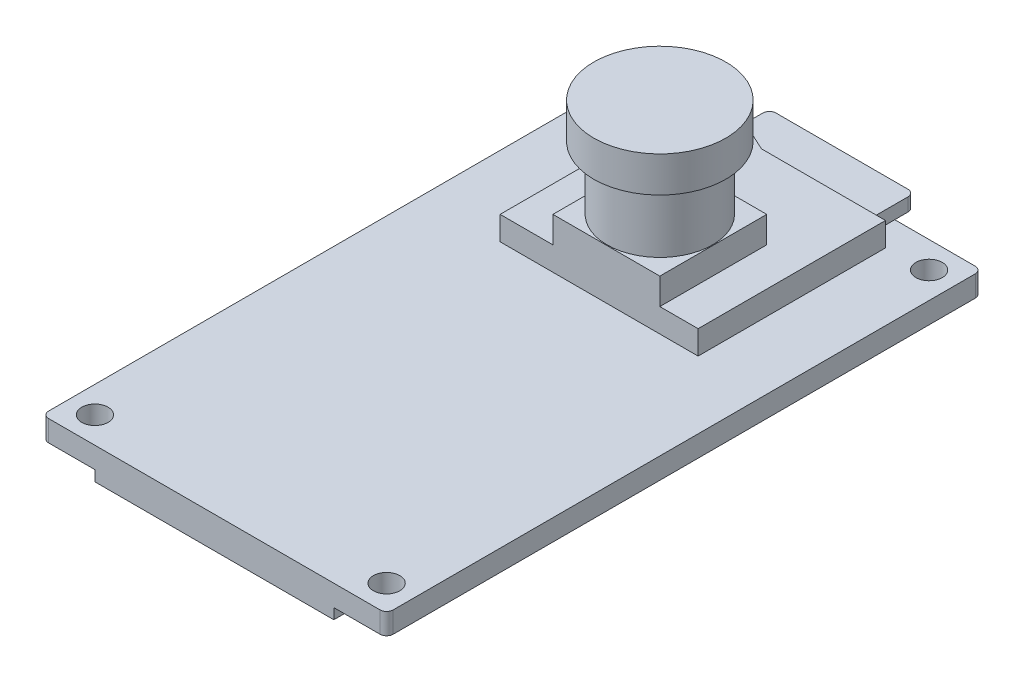
SolidWorks part; units mm, degrees
ref_plane "前视基准面" through (0, 0, 0) normal (0, 0, 1) x (1, 0, 0)
ref_plane "上视基准面" through (0, 0, 0) normal (0, 1, 0) x (1, 0, 0)
ref_plane "右视基准面" through (0, 0, 0) normal (1, 0, 0) x (0, 0, -1)
sketch "草图1" plane through (0, 0, 0) normal (0, 1, 0) x (1, 0, 0)
  line L0 (0, 60.3129) -> (0, -70.9474) construction
  line L1 (-96.3183, 0) -> (97.2298, 0) construction
  line L2 (-13.05, 22.55) -> (-13.05, -22.55)
  line L3 (-13.05, -22.55) -> (13.05, -22.55)
  line L4 (13.05, -22.55) -> (13.05, 22.55)
  line L5 (13.05, 22.55) -> (-13.05, 22.55)
  circle A0 centre (-11.05, 20.55) radius 1
  circle A1 centre (11.05, 20.55) radius 1
  circle A2 centre (-11.05, -20.55) radius 1
  circle A3 centre (11.05, -20.55) radius 1
  dimension "D5" = 2
  dimension "D1" = 26.1
  dimension "D2" = 45.1
  dimension "D3" = 22.1
  dimension "D4" = 41.1
extrude "凸台-拉伸1" add sketch "草图1" along normal blind 1.6
sketch "草图2" plane through (0, 1.6, 0) normal (0, 1, 0) x (1, 0, 0)
  line L0 (-7.05, 6.15) -> (7.95, 6.15)
  line L1 (7.95, 6.15) -> (7.95, 20.35)
  line L2 (7.95, 20.35) -> (-1.45, 20.35)
  line L3 (-1.45, 20.35) -> (-2.75, 20.95)
  line L4 (-2.75, 20.95) -> (-7.05, 20.95)
  line L5 (-7.05, 20.95) -> (-7.05, 6.15)
  line L6 (13.05, 22.55) -> (-13.05, 22.55) construction
  line L7 (13.05, -22.55) -> (13.05, 22.55) construction
  dimension "D1" = 14.2
  dimension "D2" = 14.8
  dimension "D3" = 15
  dimension "D4" = 9.4
  dimension "D5" = 4.3
  dimension "D6" = 1.6
  dimension "D7" = 5.1
extrude "凸台-拉伸2" add sketch "草图2" along normal blind 1.8
sketch "草图3" plane through (0, 0, -20.35) normal (0, 0, -1) x (-1, 0, 0)
  line L0 (-7.15, 2.3) -> (-7.15, 3.3)
  line L1 (-7.15, 3.3) -> (3.85, 3.3)
  line L2 (3.85, 3.3) -> (3.85, 2.3)
  line L3 (3.85, 2.3) -> (-7.15, 2.3)
  line L4 (-7.95, 3.4) -> (-7.95, 1.6) construction
  line L5 (-7.95, 3.4) -> (1.45, 3.4) construction
  dimension "D1" = 0.8
  dimension "D2" = 1
  dimension "D3" = 0.1
  dimension "D4" = 11
extrude "凸台-拉伸3" add sketch "草图3" along normal blind 3
fillet "圆角1" radius 0.5 6 edges at (-3.85, 2.8, -23.35) (7.15, 2.8, -23.35) (-13.05, 0.8, 22.55) (13.05, 0.8, 22.55) (13.05, 0.8, -22.55) (-13.05, 0.8, -22.55)
sketch "草图4" plane through (0, 3.4, 0) normal (0, 1, 0) x (1, 0, 0)
  line L0 (-3.05, 14.25) -> (-3.05, 6.15)
  line L1 (-3.05, 6.15) -> (5.05, 6.15)
  line L2 (5.05, 6.15) -> (5.05, 14.25)
  line L3 (5.05, 14.25) -> (-3.05, 14.25)
  line L4 (13.05, -22.05) -> (13.05, 22.05) construction
  line L5 (-13.05, 22.05) -> (-13.05, -22.05) construction
  line L6 (12.55, 22.55) -> (-12.55, 22.55) construction
  dimension "D1" = 8
  dimension "D2" = 10
  dimension "D3" = 8.1
  dimension "D4" = 8.3
extrude "凸台-拉伸4" add sketch "草图4" along normal blind 2
sketch "草图5" plane through (0, 5.4, 0) normal (0, 1, 0) x (1, 0, 0)
  line L3 (5.05, 14.25) -> (-3.05, 14.25) construction
  line L4 (-3.05, 14.25) -> (-3.05, 6.15) construction
  circle A0 centre (1, 10.2) radius 4
  dimension "D1" = 8
  dimension "D2" = 4.05
  dimension "D3" = 4.05
extrude "凸台-拉伸5" add sketch "草图5" along normal blind 4.8
sketch "草图6" plane through (0, 10.2, 0) normal (0, 1, 0) x (1, 0, 0)
  circle A0 centre (1, 10.2) radius 5
  dimension "D1" = 10
extrude "凸台-拉伸6" add sketch "草图6" along normal blind 2.7
sketch "草图7" plane through (0, 0, 0) normal (0, -1, 0) x (1, 0, 0)
  line L0 (6.55, -22.35) -> (-5.95, -22.35)
  line L1 (-5.95, -22.35) -> (-5.95, -14.65)
  line L2 (-5.95, -14.65) -> (6.55, -14.65)
  line L3 (6.55, -14.65) -> (6.55, -22.35)
  line L5 (12.55, -22.55) -> (-12.55, -22.55) construction
  line L6 (13.05, 22.05) -> (13.05, -22.05) construction
  dimension "D1" = 12.5
  dimension "D2" = 7.7
  dimension "D3" = 0.2
  dimension "D4" = 6.5
extrude "凸台-拉伸7" add sketch "草图7" along normal blind 6
sketch "草图9" plane through (0, 0, 0) normal (0, -1, 0) x (1, 0, 0)
  line L0 (6.55, -17.15) -> (6.55, -21.55)
  line L1 (6.55, -22.35) -> (6.55, -14.65) construction
  line L2 (6.55, -21.55) -> (7.75, -21.55)
  line L3 (7.75, -21.55) -> (7.75, -17.15)
  line L4 (7.75, -17.15) -> (6.55, -17.15)
  line L5 (-5.95, -17.15) -> (-7.15, -17.15)
  line L6 (-5.95, -14.65) -> (-5.95, -22.35) construction
  line L7 (-7.15, -17.15) -> (-7.15, -21.55)
  line L8 (-7.15, -21.55) -> (-5.95, -21.55)
  line L9 (-5.95, -21.55) -> (-5.95, -17.15)
  dimension "D1" = 1.2
  dimension "D2" = 4.4
  dimension "D3" = 0.8
extrude "凸台-拉伸8" add sketch "草图9" along normal blind 2.9
sketch "草图10" plane through (0, 0, 0) normal (0, -1, 0) x (1, 0, 0)
  line L0 (9.05, 22.55) -> (-9.05, 22.55)
  line L1 (-12.55, 22.55) -> (12.55, 22.55) construction
  line L2 (-9.05, 22.55) -> (-9.05, -2.95)
  line L3 (-9.05, -2.95) -> (9.05, -2.95)
  line L4 (9.05, -2.95) -> (9.05, 22.55)
  line L5 (13.05, 22.05) -> (13.05, -22.05) construction
  line L7 (-13.05, -22.05) -> (-13.05, 22.05) construction
  dimension "D1" = 4
  dimension "D2" = 4
  dimension "D3" = 25.5
extrude "凸台-拉伸9" add sketch "草图10" along normal blind 0.8
sketch "草图11" plane through (0, -0.8, 0) normal (0, -1, 0) x (1, 0, 0)
  line L0 (-7.98, 15.86) -> (7.88, 15.86)
  line L1 (7.88, 15.86) -> (7.88, -1.88)
  line L2 (7.88, -1.88) -> (-7.98, -1.88)
  line L3 (-7.98, -1.88) -> (-7.98, 15.86)
  line L4 (-9.05, 22.55) -> (-9.05, -2.95) construction
  line L10 (-9.05, -2.95) -> (9.05, -2.95) construction
  dimension "D1" = 15.86
  dimension "D2" = 17.74
  dimension "D3" = 1.07
  dimension "D4" = 1.07
extrude "凸台-拉伸10" add sketch "草图11" along normal blind 2.3
sketch "草图12" plane through (0, 0, 0) normal (0, -1, 0) x (1, 0, 0)
  line L0 (-11.9, 17.55) -> (-11.02, 17.55)
  line L1 (-11.02, 17.55) -> (-11.02, 15.55)
  line L2 (-11.02, 15.55) -> (-11.9, 15.55)
  line L3 (-11.9, 15.55) -> (-11.9, 17.55)
  line L4 (-13.05, -22.05) -> (-13.05, 22.05) construction
  line L5 (-12.55, 22.55) -> (-9.05, 22.55) construction
  line L6 (-11.9, 14.55) -> (-11.02, 14.55)
  line L7 (-11.02, 14.55) -> (-11.02, 12.55)
  line L8 (-11.02, 12.55) -> (-11.9, 12.55)
  line L9 (-11.9, 12.55) -> (-11.9, 14.55)
  line L10 (-11.9, 11.55) -> (-11.02, 11.55)
  line L11 (-11.02, 11.55) -> (-11.02, 9.55)
  line L12 (-11.02, 9.55) -> (-11.9, 9.55)
  line L13 (-11.9, 9.55) -> (-11.9, 11.55)
  line L14 (-11.9, 8.55) -> (-11.02, 8.55)
  line L15 (-11.02, 8.55) -> (-11.02, 6.55)
  line L16 (-11.02, 6.55) -> (-11.9, 6.55)
  line L17 (-11.9, 6.55) -> (-11.9, 8.55)
  line L18 (-11.9, 5.55) -> (-11.02, 5.55)
  line L19 (-11.02, 5.55) -> (-11.02, 3.55)
  line L20 (-11.02, 3.55) -> (-11.9, 3.55)
  line L21 (-11.9, 3.55) -> (-11.9, 5.55)
  dimension "D1" = 0.88
  dimension "D2" = 1.15
  dimension "D3" = 2
  dimension "D4" = 5
  dimension "D5" = 5
extrude "凸台-拉伸11" add sketch "草图12" along normal blind 0.8
